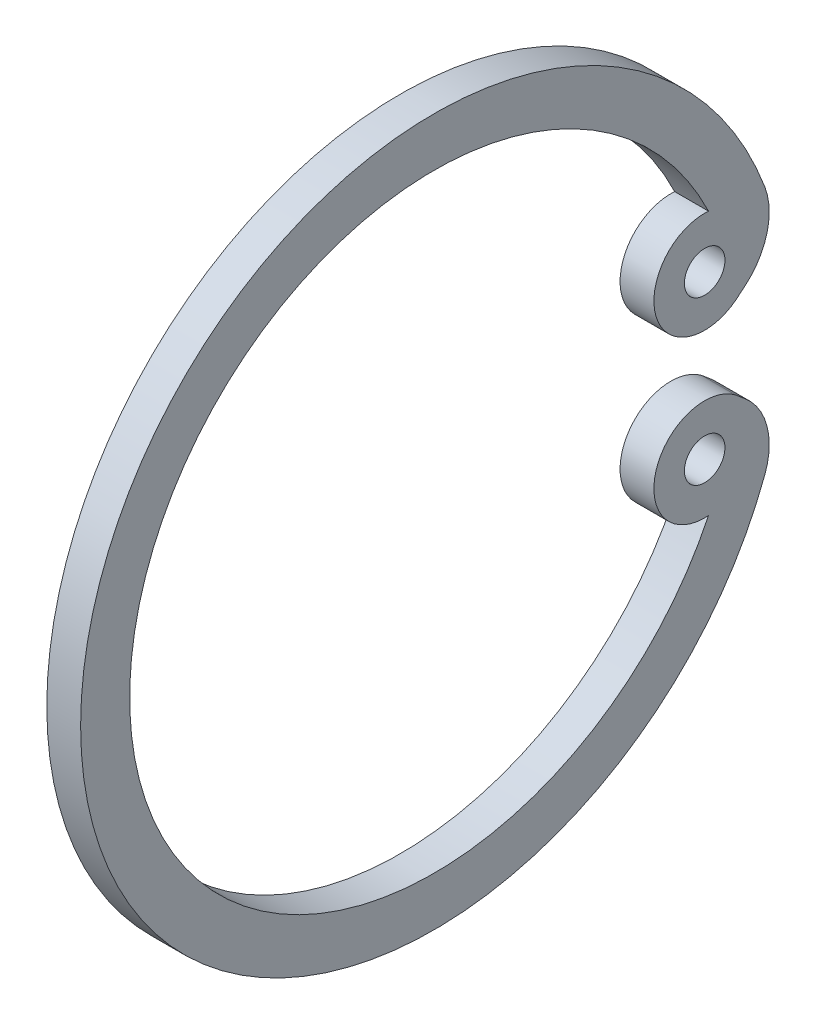
SolidWorks part; units mm, degrees
ref_plane "Front Plane" through (0, 0, 0) normal (0, 0, 1) x (1, 0, 0)
ref_plane "Top Plane" through (0, 0, 0) normal (0, 1, 0) x (1, 0, 0)
ref_plane "Right Plane" through (0, 0, 0) normal (1, 0, 0) x (0, 0, -1)
ref_plane "Plane1" through (19, 0, 0) normal (1, 0, 0) x (0, 0, -1)
sketch "Sketch1" plane through (19, 0, 0) normal (1, 0, 0) x (0, 0, -1)
  line L0 (-1.0829, 1.2142) -> (-0.8063, 1.4448)
  line L1 (-0.8063, -1.4451) -> (-1.0822, -1.2136)
  arc A0 (-1.8869, 3.8965) -> (-1.0829, 1.2142) centre (-2.0005, 2.4008) ccw
  arc A1 (-0.8063, 1.4448) -> (-0.2201, 3.6816) centre (-2.0918, 2.9769) ccw
  arc A2 (-0.2201, 3.6816) -> (-0.2201, -3.6818) centre (-9.9996, -0.0001) ccw
  arc A3 (-0.2201, -3.6818) -> (-0.8063, -1.4451) centre (-2.0918, -2.9772) ccw
  arc A4 (-1.0822, -1.2136) -> (-1.8869, -3.8967) centre (-2.0004, -2.4004) ccw
  arc A5 (-1.8869, -3.8967) -> (-1.8869, 3.8965) centre (-9.9996, -0.0001) cw
  circle A6 centre (-2, -2.4) radius 0.6
  circle A7 centre (-2, 2.4) radius 0.6
extrude "Boss-Extrude1" add sketch "Sketch1" against normal blind 1
scale "Scale1" scale about centroid uniform scaling yes scale factor 0.222222
scale "Scale2" scale about centroid uniform scaling yes scale factor 1.25
